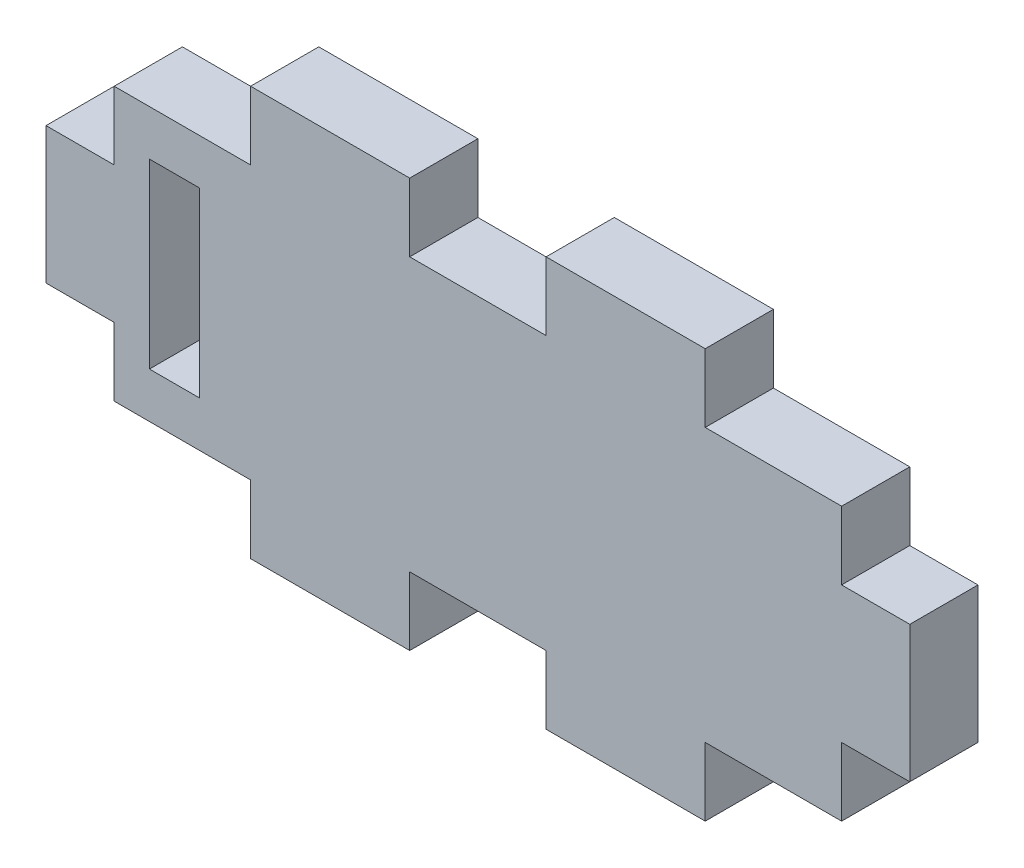
SolidWorks part; units mm, degrees
ref_plane "Front Plane" through (0, 0, 0) normal (0, 0, 1) x (1, 0, 0)
ref_plane "Top Plane" through (0, 0, 0) normal (0, 1, 0) x (1, 0, 0)
ref_plane "Right Plane" through (0, 0, 0) normal (1, 0, 0) x (0, 0, -1)
sketch "Sketch2" plane through (0, 0, 0) normal (0, 0, 1) x (1, 0, 0)
  line L0 (-31.1579, 0) -> (35.1345, 0) construction
  line L1 (0, 28.4678) -> (0, -29.6374) construction
  line L3 (-16, 6) -> (16, 6)
  line L4 (-16, 6) -> (-16, -6)
  line L5 (-16, -6) -> (16, -6)
  line L6 (16, 6) -> (16, -6)
  dimension "D1" = 16
  dimension "D2" = 16
  dimension "D3" = 6
  dimension "D4" = 6
extrude "Boss-Extrude1" add sketch "Sketch2" along normal blind 3
sketch "Sketch3" plane through (0, 0, 3) normal (0, 0, 1) x (1, 0, 0)
  line L0 (0, 12.0409) -> (0, -11.2481) construction
  line L1 (-19.9591, 0) -> (20.4348, 0) construction
  line L2 (-16, -6) -> (16, -6) construction
  line L3 (-3, -6) -> (-10, -6)
  line L4 (-3, -6) -> (-3, -9)
  line L5 (-3, -9) -> (-10, -9)
  line L6 (-10, -6) -> (-10, -9)
  line L7 (10, -6) -> (10, -9)
  line L8 (3, -9) -> (10, -9)
  line L9 (3, -6) -> (3, -9)
  line L10 (3, -6) -> (10, -6)
  line L11 (3, 6) -> (10, 6)
  line L12 (3, 6) -> (3, 9)
  line L13 (3, 9) -> (10, 9)
  line L14 (10, 6) -> (10, 9)
  line L15 (-10, 6) -> (-10, 9)
  line L16 (-3, 9) -> (-10, 9)
  line L17 (-3, 6) -> (-3, 9)
  line L18 (-3, 6) -> (-10, 6)
  line L19 (-16, 6) -> (-16, -6) construction
  line L20 (-16, 3) -> (-19, 3)
  line L21 (-16, 3) -> (-16, -3)
  line L22 (-16, -3) -> (-19, -3)
  line L23 (-19, 3) -> (-19, -3)
  line L24 (19, 3) -> (19, -3)
  line L25 (16, -3) -> (19, -3)
  line L26 (16, 3) -> (16, -3)
  line L27 (16, 3) -> (19, 3)
  point P29 (-17.5, 3)
  dimension "D1" = 3
  dimension "D2" = 7
  dimension "D3" = 3
  dimension "D4" = 3
  dimension "D5" = 3
  dimension "D6" = 3
extrude "Boss-Extrude3" add sketch "Sketch3" against normal blind 3
sketch "Sketch4" plane through (0, 0, 3) normal (0, 0, 1) x (1, 0, 0)
  line L0 (-21.3948, 0) -> (22.6423, 0) construction
  line L3 (-12.25, 4) -> (-14.45, 4)
  line L4 (-12.25, 4) -> (-12.25, -4)
  line L5 (-12.25, -4) -> (-14.45, -4)
  line L6 (-14.45, 4) -> (-14.45, -4)
  point P3 (0, 0)
  point P9 (-13.35, -4)
  dimension "D1" = 12.25
  dimension "D2" = 8
  dimension "D3" = 4
  dimension "D4" = 2.2
extrude "Cut-Extrude1" cut sketch "Sketch4" against normal blind 3
